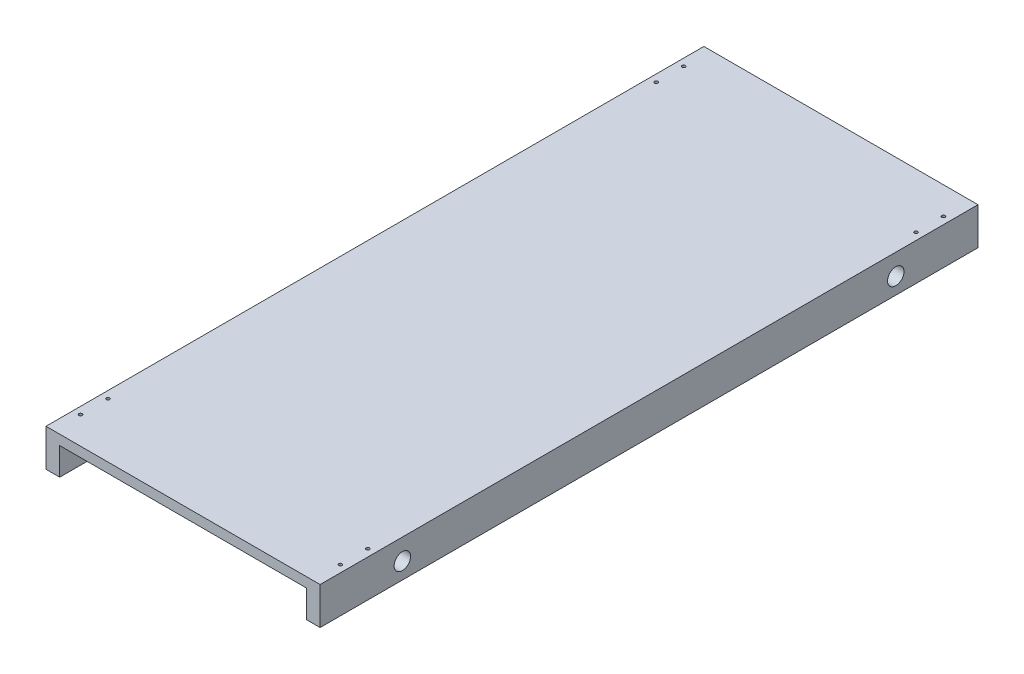
SolidWorks part; units mm, degrees
ref_plane "Front Plane" through (0, 0, 0) normal (0, 0, 1) x (1, 0, 0)
ref_plane "Top Plane" through (0, 0, 0) normal (0, 1, 0) x (1, 0, 0)
ref_plane "Right Plane" through (0, 0, 0) normal (1, 0, 0) x (0, 0, -1)
sketch "Sketch1" plane through (0, 0, 0) normal (0, 0, 1) x (1, 0, 0)
  line L1 (0, 0) -> (500, 0)
  line L2 (0, 0) -> (0, 18)
  line L3 (0, 18) -> (500, 18)
  line L4 (500, 0) -> (500, 18)
  line L5 (0, 0) -> (25, 0)
  line L6 (0, 0) -> (0, -50)
  line L7 (0, -50) -> (25, -50)
  line L8 (25, 0) -> (25, -50)
  line L9 (500, 0) -> (475, 0)
  line L10 (500, 0) -> (500, -50)
  line L11 (500, -50) -> (475, -50)
  line L12 (475, 0) -> (475, -50)
  dimension "D1" = 68
  dimension "D2" = 25
  dimension "D3" = 18
  dimension "D4" = 25
  dimension "D5" = 500
extrude "Boss-Extrude1" add sketch "Sketch1" along normal blind 1200 contours L8 L1 L6 L7 | L1 L4 L3 L2 | L1 L12 L11 L10
sketch "Sketch2" plane through (500, 0, 0) normal (1, 0, 0) x (0, 0, -1)
  line L0 (0, -50) -> (0, 18) construction
  line L1 (-1200, -50) -> (0, -50) construction
  line L2 (-1200, -50) -> (-1200, 18) construction
  circle A0 centre (-1050, -20) radius 15
  circle A1 centre (-150, -20) radius 15
  dimension "D1" = 30
  dimension "D2" = 150
  dimension "D3" = 30
  dimension "D4" = 150
extrude "Cut-Extrude1" cut sketch "Sketch2" against normal through all both and the other way through all
hole_wizard "Ø6.0 (6) Diameter Hole1" positions "Sketch3" profile "Sketch4" hole size "Ø6.0" standard "ISO" end condition through all
sketch "Sketch3" plane through (0, 18, 0) normal (0, 1, 0) x (1, 0, 0)
  line L0 (0, -1200) -> (500, -1200) construction
  line L3 (0, -1200) -> (0, 0) construction
  point P0 (13, -1150)
  point P9 (0, -1157.8982)
  dimension "D1" = 50
  dimension "D2" = 13
sketch "Sketch4" plane through (13, 18, 1150) normal (1, 0, 0) x (0, 0, 1)
  line L0 (0, 0) -> (0, 68)
  line L1 (0, 68) -> (3, 68)
  line L2 (3, 68) -> (3, 0)
  line L5 (3, 0) -> (0, 0)
  line L11 (0, -6.35) -> (0, 107.95) construction
  dimension "Thru Hole Dia." = 6
  dimension "Thru Hole Depth" = 68
pattern_linear "LPattern1" count 2 spacing 50 along (0, 0, -1) count 2 spacing 474 along (1, 0, 0) of "Ø6.0 (6) Diameter Hole1"
pattern_linear "LPattern2" count 2 spacing 1050 along (0, 0, -1) of "LPattern1", "Ø6.0 (6) Diameter Hole1"
